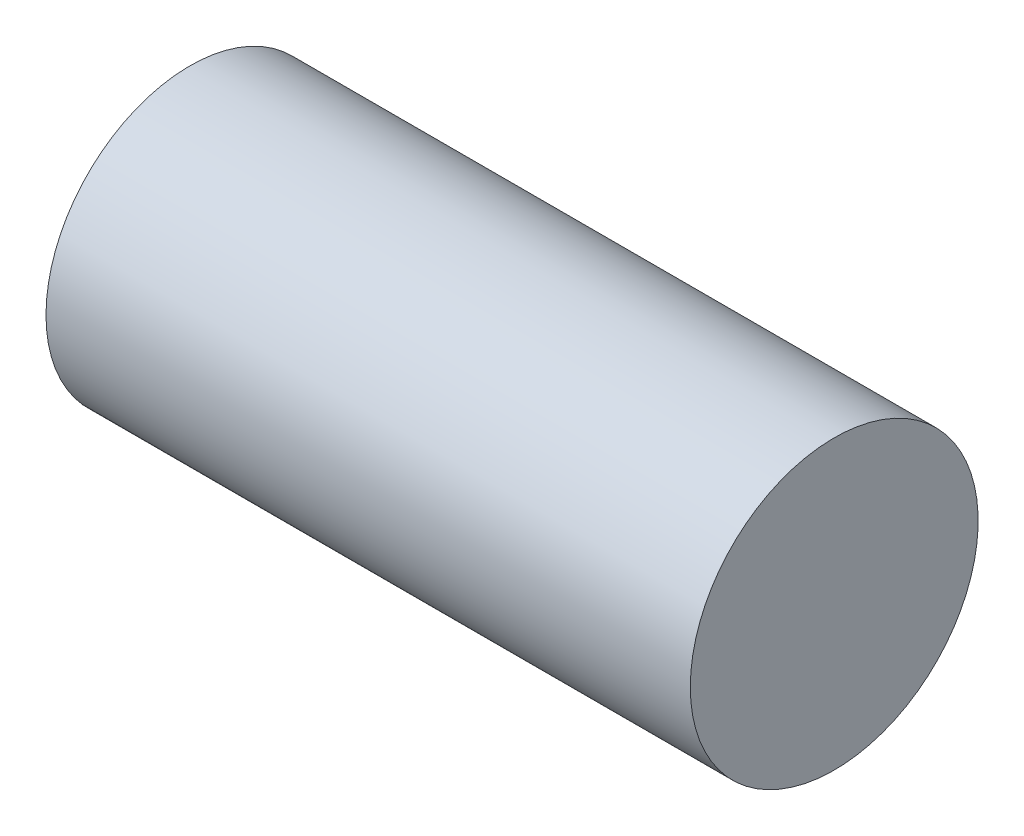
SolidWorks part; units mm, degrees
ref_plane "前视基准面" through (0, 0, 0) normal (0, 0, 1) x (1, 0, 0)
ref_plane "上视基准面" through (0, 0, 0) normal (0, 1, 0) x (1, 0, 0)
ref_plane "右视基准面" through (0, 0, 0) normal (1, 0, 0) x (0, 0, -1)
sketch "草图1" plane through (56.7207, 0, 0) normal (-1, 0, 0) x (0, 0, 1)
  circle A0 centre (61.708, -76.6302) radius 13.4031
extrude "凸台-拉伸1" add sketch "草图1" along normal blind 60
